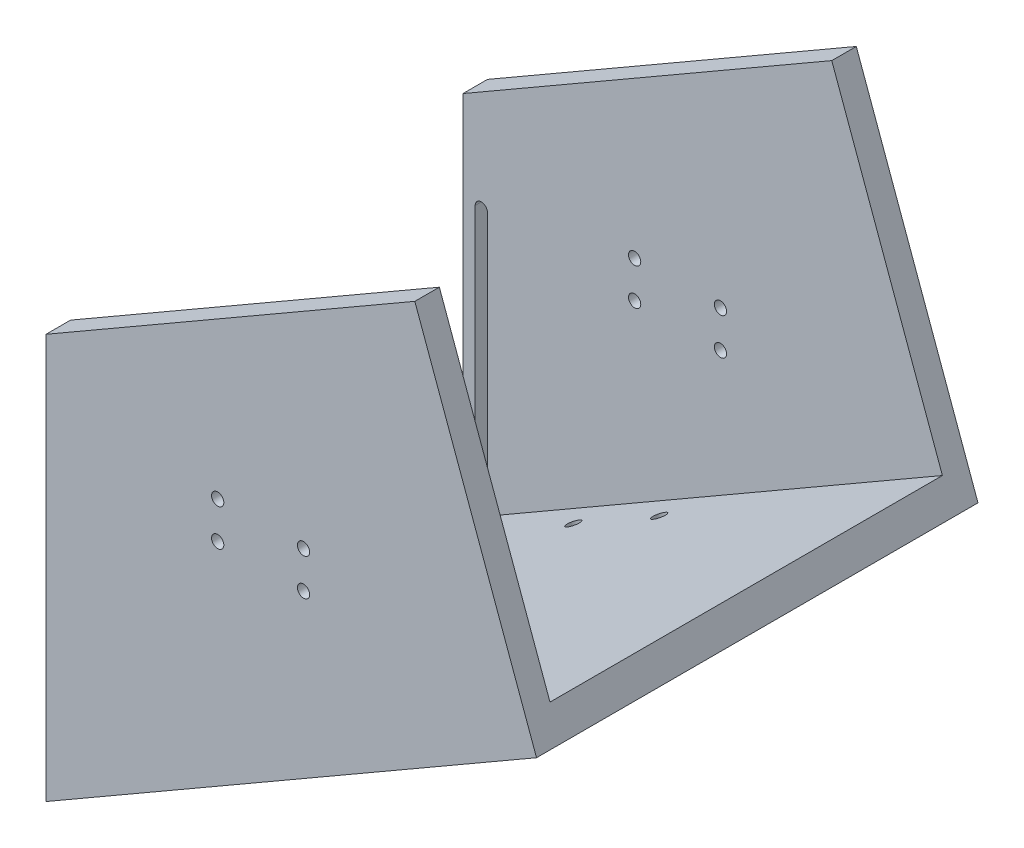
SolidWorks part; units mm, degrees
material "Acrylic (Medium-high impact)"
ref_plane "Front Plane" through (0, 0, 0) normal (0, 0, 1) x (1, 0, 0)
ref_plane "Top Plane" through (0, 0, 0) normal (0, 1, 0) x (1, 0, 0)
ref_plane "Right Plane" through (0, 0, 0) normal (1, 0, 0) x (0, 0, -1)
sketch "Sketch1" plane through (0, 0, 0) normal (0, 1, 0) x (1, 0, 0)
  line L0 (0, 75) -> (50, 75)
  line L1 (0, 90) -> (250, 90)
  line L2 (0, 90) -> (0, -90)
  line L3 (0, -90) -> (250, -90)
  line L4 (250, 90) -> (250, -90)
  line L9 (50, 75) -> (50, -75)
  line L10 (50, -75) -> (0, -75)
  circle A0 centre (7.5, 67.5) radius 2.5
  circle A1 centre (42.5, 67.5) radius 2.5
  circle A2 centre (7.5, -67.5) radius 2.5
  circle A3 centre (42.5, -67.5) radius 2.5
  dimension "D8" = 5
  dimension "D9" = 5
  dimension "D14" = 5
  dimension "D15" = 5
  dimension "D1" = 180
  dimension "D2" = 250
  dimension "D3" = 150
  dimension "D4" = 15
  dimension "D5" = 50
  dimension "D6" = 0
  dimension "D7" = 75
  dimension "D10" = 7.5
  dimension "D11" = 7.5
  dimension "D12" = 7.5
  dimension "D13" = 7.5
  dimension "D16" = 7.5
  dimension "D17" = 7.5
  dimension "D18" = 7.5
  dimension "D19" = 7.5
extrude "Boss-Extrude1" add sketch "Sketch1" along normal blind 15 contours L9 L10 L2 L3 L4 L1 L0 | L10 L9 L0 L2 A3 A2 A1 A0
sketch "Sketch2" plane through (0, 0, 0) normal (0, 0, 1) x (1, 0, 0)
  line L0 (0, 0) -> (-200, -115.4701)
  line L1 (0, 15) -> (-200, -100.4701)
  line L2 (0, 0) -> (0, 15)
  line L3 (-200, -100.4701) -> (-200, -115.4701)
  dimension "D1" = 120
  dimension "D2" = 200
extrude "Boss-Extrude2" add sketch "Sketch2" along normal mid plane 180
sketch "Sketch3" plane through (0, 15, 0) normal (0, 1, 0) x (1, 0, 0)
  line L0 (0, 75) -> (250, 75)
  line L1 (0, 90) -> (0, -90) construction
  line L2 (250, 90) -> (250, -90) construction
  line L3 (250, 75) -> (250, 90)
  line L4 (250, 90) -> (0, 90)
  line L5 (0, 90) -> (250, 90) construction
  line L6 (0, 90) -> (0, 75)
  line L7 (0, -90) -> (0, -75)
  line L8 (0, -75) -> (250, -75)
  line L9 (250, -75) -> (250, -90)
  line L10 (250, -90) -> (0, -90)
  dimension "D1" = 15
  dimension "D2" = 15
extrude "Boss-Extrude3" add sketch "Sketch3" along normal blind 150 contours L6 L0 L3 L4 | L10 L7 L8 L9
sketch "Sketch8" plane through (0, 0, 90) normal (0, 0, 1) x (1, 0, 0)
  line L0 (0, 15) -> (-200, -100.4701)
  line L1 (-200, -100.4701) -> (-200, 49.5299)
  line L2 (-200, 49.5299) -> (0, 165)
  line L3 (0, 165) -> (0, 15)
extrude "Boss-Extrude8" add sketch "Sketch8" against normal blind 10
mirror "Mirror1" about plane through (0, 0, 0) normal (0, 0, 1) of "Boss-Extrude8"
sketch "Sketch9" plane through (0, 0, -75) normal (0, 0, 1) x (1, 0, 0)
  line L0 (-192.5, 12.5203) -> (-192.5, -87.4797) construction
  line L1 (-190, 12.5203) -> (-190, -87.4797)
  line L2 (-195, 12.5203) -> (-195, -87.4797)
  line L5 (-200, -100.4701) -> (0, 15) construction
  line L6 (-200, 49.5299) -> (-200, -115.4701) construction
  arc A0 (-190, 12.5203) -> (-195, 12.5203) centre (-192.5, 12.5203) ccw
  arc A1 (-195, -87.4797) -> (-190, -87.4797) centre (-192.5, -87.4797) ccw
  point P2 (-192.5, -37.4797)
  dimension "D3" = 7.5
  dimension "D4" = 100
  dimension "D1" = 5
  dimension "D2" = 5
extrude "Cut-Extrude1" cut sketch "Sketch9" against normal blind 10
mirror "Mirror2" about plane through (0, 0, 0) normal (0, 0, 1) of "Cut-Extrude1"
sketch "Sketch10" plane through (250, 0, 0) normal (1, 0, 0) x (0, 0, -1)
  line L5 (-90, 165) -> (25, 165)
  line L6 (25, 165) -> (25, 0)
  line L7 (90, 0) -> (-90, 0) construction
  line L8 (25, 0) -> (-90, 0)
  line L9 (-90, 0) -> (-90, 165)
  dimension "D1" = 115
extrude "Boss-Extrude12" add sketch "Sketch10" against normal blind 15
mirror "Mirror3" about plane through (0, 0, 0) normal (0, 0, 1) of "Boss-Extrude12"
sketch "Sketch12" plane through (0, 0, 90) normal (0, 0, 1) x (1, 0, 0)
  line L1 (0, 165) -> (250, 165)
  line L7 (250, 165) -> (250, 0)
  line L8 (250, 0) -> (0, 0)
  line L11 (0, 165) -> (-49.6266, 136.3481)
  line L12 (0, 165) -> (-200, 49.5299) construction
  line L13 (-49.6266, 136.3481) -> (0, 0)
  line L14 (-200, -115.4701) -> (0, 0) construction
  dimension "D1" = 100
extrude "Cut-Extrude3" cut sketch "Sketch12" against normal through all
sketch "Sketch13" plane through (0, 0, 0) normal (0, 1, 0) x (1, 0, 0)
  line L0 (-100, 75) -> (-100, -75) construction
  line L1 (-200, -80) -> (-200, 80) construction
  line L2 (-100, 75) -> (-150, 75) construction
  line L3 (-150, 75) -> (-150, -75) construction
  line L4 (-150, -75) -> (-100, -75) construction
  circle A0 centre (-142.5, 67.5) radius 2.5
  circle A1 centre (-107.5, 67.5) radius 2.5
  circle A2 centre (-142.5, -67.5) radius 2.5
  circle A3 centre (-107.5, -67.5) radius 2.5
  point P4 (-142.5, 67.5)
  point P7 (-107.5, 67.5)
  point P9 (-107.5, -67.5)
  point P10 (-142.5, -67.5)
  dimension "D13" = 5
  dimension "D14" = 5
  dimension "D15" = 5
  dimension "D16" = 5
  dimension "D2" = 150
  dimension "D3" = 75
  dimension "D4" = 50
  dimension "D5" = 7.5
  dimension "D6" = 7.5
  dimension "D7" = 7.5
  dimension "D8" = 7.5
  dimension "D9" = 7.5
  dimension "D10" = 7.5
  dimension "D11" = 7.5
  dimension "D12" = 7.5
  dimension "D17" = 50
extrude "Cut-Extrude4" cut sketch "Sketch13" against normal through all
sketch "Sketch14" plane through (0, 0, -90) normal (0, 0, -1) x (-1, 0, 0)
  circle A0 centre (95, 11.3481) radius 2.5
  circle A1 centre (130, 11.3481) radius 2.5
  circle A2 centre (95, 26.3481) radius 2.5
  circle A3 centre (130, 26.3481) radius 2.5
  dimension "D1" = 5
  dimension "D2" = 5
  dimension "D3" = 5
  dimension "D4" = 5
  dimension "D5" = 35
  dimension "D6" = 70
  dimension "D7" = 15
  dimension "D8" = 15
  dimension "D9" = 35
  dimension "D10" = 110
extrude "Cut-Extrude5" cut sketch "Sketch14" against normal through all
